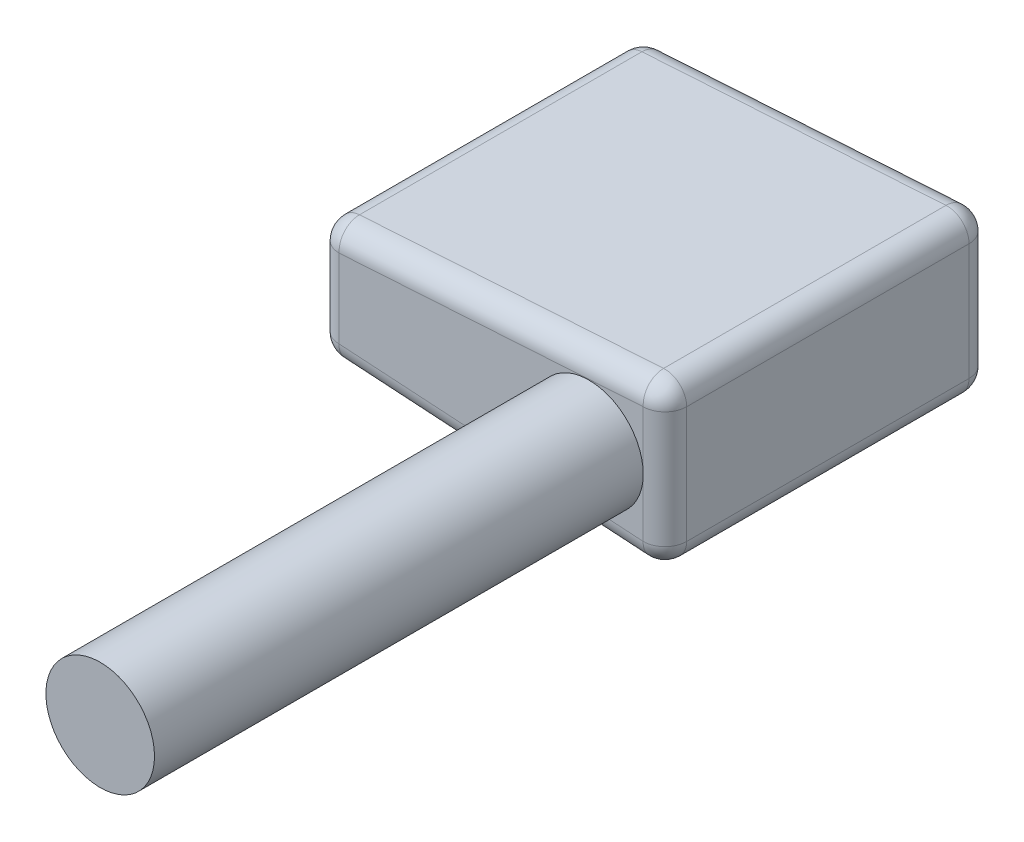
SolidWorks part; units mm, degrees
ref_plane "Plano frontal" through (0, 0, 0) normal (0, 0, 1) x (1, 0, 0)
ref_plane "Plano superior" through (0, 0, 0) normal (0, 1, 0) x (1, 0, 0)
ref_plane "Plano direito" through (0, 0, 0) normal (1, 0, 0) x (0, 0, -1)
sketch "Esboço2" plane through (0, 0, 0) normal (0, 0, 1) x (1, 0, 0)
  line L0 (0, 0) -> (0, 15)
  line L3 (-32, 13) -> (0, 15)
  line L7 (-32, 2) -> (0, 0)
  line L9 (-32, 13) -> (-32, 2)
extrude "Ressalto-extrusão1" add sketch "Esboço2" along normal blind 30
fillet "Filete1" radius 2 12 edges at (-16, 1, 0) (0, 0, 15) (0, 7.5, 0) (-16, 1, 30) (0, 7.5, 30) (0, 15, 15) (-16, 14, 0) (-16, 14, 30) (-32, 7.5, 30) (-32, 2, 15) (-32, 7.5, 0) (-32, 13, 15)
sketch "Esboço4" plane through (0, 0, 30) normal (0, 0, 1) x (1, 0, 0)
  circle A0 centre (-7, 7.5) radius 5
extrude "Ressalto-extrusão2" add sketch "Esboço4" along normal blind 45
